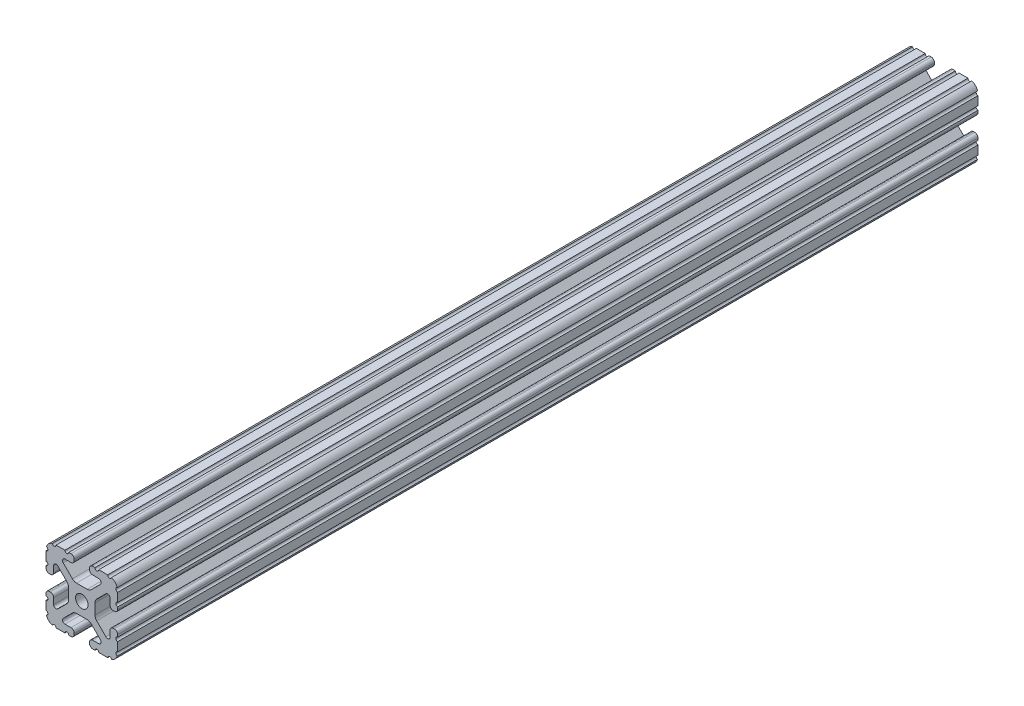
SolidWorks part; units mm, degrees
ref_plane "Front Plane" through (0, 0, 0) normal (0, 0, 1) x (1, 0, 0)
ref_plane "Top Plane" through (0, 0, 0) normal (0, 1, 0) x (1, 0, 0)
ref_plane "Right Plane" through (0, 0, 0) normal (1, 0, 0) x (0, 0, -1)
sketch "Sketch2" plane through (0, 0, 0) normal (0, 0, 1) x (1, 0, 0)
  line L0 (0, 19.05) -> (0, -19.05) construction
  line L1 (-19.05, 0) -> (19.05, 0) construction
  line L2 (4.064, -19.05) -> (19.05, -19.05)
  line L3 (19.05, -19.05) -> (19.05, -4.064)
  line L4 (4.064, -19.05) -> (4.064, -14.986)
  line L5 (4.064, -14.986) -> (12.1123, -14.986)
  line L6 (12.1123, -14.986) -> (4.1113, -6.985)
  line L7 (0, 0) -> (19.05, -19.05) construction
  line L8 (19.05, -4.064) -> (14.986, -4.064)
  line L9 (14.986, -4.064) -> (14.986, -12.1123)
  line L10 (14.986, -12.1123) -> (6.985, -4.1113)
  circle A0 centre (0, 0) radius 3.3274
  arc A1 (8.9963, -14.986) -> (9.909, -12.7826) centre (8.9963, -13.6953) ccw construction
  point P8 (0, -6.985)
  dimension "Center Hole Diameter" = 6.6548
  dimension "Rail Height" = 38.1
  dimension "Rail Width" = 38.1
  dimension "T-Slot Width" = 8.128
  dimension "Slot Inner Width" = 20.574
  dimension "Thickness" = 4.064
  dimension "Slot Depth" = 8.001
  dimension "D1" = 4.064
sketch "Sketch3" plane through (0, 0, 0) normal (1, 0, 0) x (0, 0, -1)
  line L0 (-228.6, -19.05) -> (228.6, -19.05) construction
  line L1 (-205.74, 0) -> (205.74, 0) construction
  dimension "Length" = 457.2
  dimension "D1" = 411.48
sketch "Sketch4" plane through (0, 0, 0) normal (0, 0, 1) x (1, 0, 0)
  line L0 (5.7912, -19.05) -> (14.3002, -19.05)
  line L1 (4.064, -19.05) -> (19.05, -19.05) construction
  line L2 (4.064, -19.05) -> (4.064, -14.986) construction
  line L3 (4.064, -14.986) -> (12.1123, -14.986) construction
  line L4 (4.064, -16.7132) -> (4.064, -17.3228)
  line L5 (5.7912, -14.986) -> (8.9963, -14.986)
  line L6 (0, -6.985) -> (2.833, -6.985)
  line L7 (12.1123, -14.986) -> (4.1113, -6.985) construction
  line L8 (5.0152, -7.8889) -> (9.909, -12.7826)
  line L9 (19.05, -19.05) -> (19.05, -4.064) construction
  line L10 (14.986, -12.1123) -> (6.985, -4.1113) construction
  line L11 (14.986, -4.064) -> (14.986, -12.1123) construction
  line L12 (14.986, -8.9963) -> (14.986, -5.7912)
  line L13 (19.05, -4.064) -> (14.986, -4.064) construction
  line L14 (16.7132, -4.064) -> (17.3228, -4.064)
  line L15 (19.05, -5.7912) -> (19.05, -14.3002)
  line L16 (12.7826, -9.909) -> (7.8889, -5.0152)
  line L17 (6.985, 0) -> (6.985, -2.833)
  line L18 (-19.05, 0) -> (19.05, 0) construction
  line L19 (0, -6.985) -> (0, -3.3274)
  line L20 (0, 19.05) -> (0, -19.05) construction
  line L21 (6.985, 0) -> (3.3274, 0)
  arc A0 (4.064, -17.3228) -> (5.7912, -19.05) centre (5.7912, -17.3228) ccw
  arc A2 (4.064, -16.7132) -> (5.7912, -14.986) centre (5.7912, -16.7132) cw
  arc A3 (8.9963, -14.986) -> (9.909, -12.7826) centre (8.9963, -13.6953) ccw
  arc A4 (2.833, -6.985) -> (5.0152, -7.8889) centre (2.833, -10.0711) cw
  arc A5 (14.3002, -19.05) -> (19.05, -14.3002) centre (14.3002, -14.3002) ccw
  arc A6 (12.7826, -9.909) -> (14.986, -8.9963) centre (13.6953, -8.9963) ccw
  arc A7 (14.986, -5.7912) -> (16.7132, -4.064) centre (16.7132, -5.7912) cw
  arc A8 (17.3228, -4.064) -> (19.05, -5.7912) centre (17.3228, -5.7912) cw
  arc A9 (7.8889, -5.0152) -> (6.985, -2.833) centre (10.0711, -2.833) cw
  circle A10 centre (0, 0) radius 3.3274 construction
  arc A11 (0, -3.3274) -> (3.3274, 0) centre (0, 0) ccw
  dimension "D1" = 4.7498
  dimension "D2" = 3.0861
  dimension "D3" = 1.7272
extrude "Boss-Extrude1" add sketch "Sketch4" along normal mid plane 457.2
sketch "Sketch5" plane through (0, 0, 0) normal (0, 0, 1) x (1, 0, 0)
  line L0 (4.064, -19.05) -> (19.05, -19.05) construction
  line L1 (5.7912, -14.986) -> (8.9963, -14.986) construction
  line L3 (0, 0) -> (19.05, -19.05) construction
  line L4 (8.9963, -14.986) -> (8.9963, -19.05) construction
  line L5 (12.1123, -14.986) -> (4.1113, -6.985) construction
  circle A0 centre (14.7395, -19.05) radius 1.016
  circle A1 centre (7.9803, -19.05) radius 1.016
  circle A2 centre (19.05, -14.7395) radius 1.016
  circle A3 centre (19.05, -7.9803) radius 1.016
  point P10 (7.3938, -14.986)
  point P12 (13.6953, -8.9963)
  dimension "D1" = 2.032
extrude "Cut-Extrude1" cut sketch "Sketch5" against normal through all both and the other way through all
mirror "Mirror1" about plane through (0, 0, 0) normal (1, 0, 0) of bodies 137 134
mirror "Mirror2" about plane through (0, 0, 0) normal (0, 1, 0) of bodies 135
equation "\"D1@Boss-Extrude1\"=\"Length@Sketch3\""
equation "\"D1@Sketch2\"=\"Thickness@Sketch2\""
equation "\"D2@Sketch4\"=\"Slot Inner Width@Sketch2\"*0.15"
equation "\"D1@Sketch4\"=\"D3@Sketch4\"*2.75"
equation "\"D3@Sketch4\"=\"Thickness@Sketch2\"*0.425"
equation "\"D1@Sketch5\"=\"Thickness@Sketch2\"*0.5"
equation "\"D1@Sketch3\"=\"Length@Sketch3\"*0.9"
